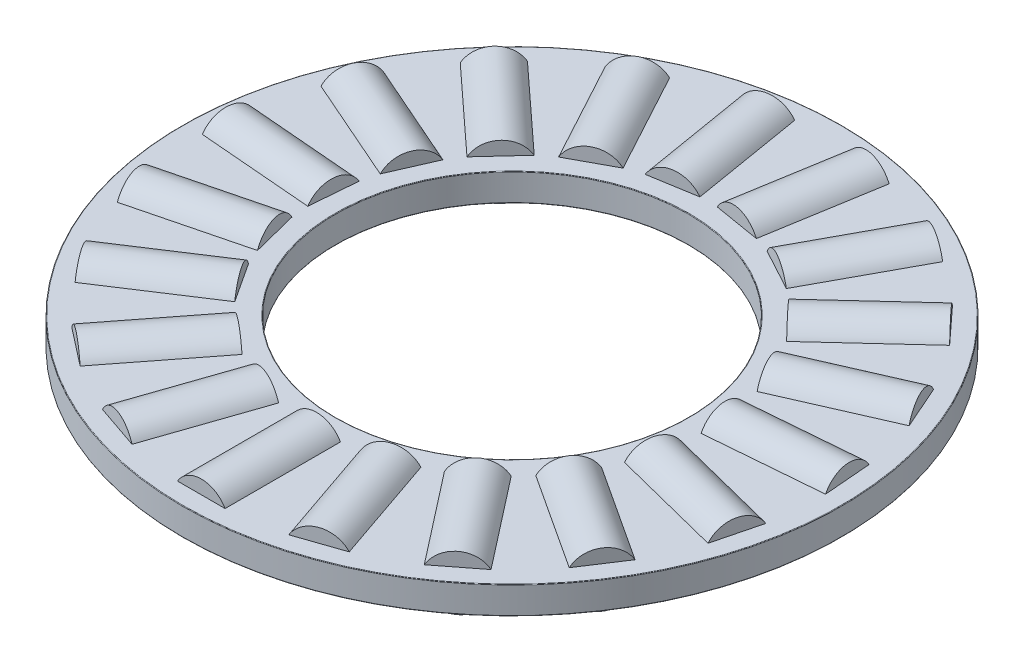
SolidWorks part; units mm, degrees
ref_plane "Front Plane" through (0, 0, 0) normal (0, 0, 1) x (1, 0, 0)
ref_plane "Top Plane" through (0, 0, 0) normal (0, 1, 0) x (1, 0, 0)
ref_plane "Right Plane" through (0, 0, 0) normal (1, 0, 0) x (0, 0, -1)
sketch "Sketch1" plane through (0, 0, 0) normal (1, 0, 0) x (0, 0, -1)
  line L0 (-11.9062, 0) -> (11.9062, 0) construction
  line L1 (0, -0.9922) -> (0, 0.9922) construction
  line L2 (-11.9063, 0.4961) -> (-6.3754, 0.4961)
  line L3 (-11.9063, 0.4961) -> (-11.9063, -0.4961)
  line L4 (-11.9063, -0.4961) -> (-6.3754, -0.4961)
  line L5 (-6.3754, 0.4961) -> (-6.3754, -0.4961)
  line L7 (-9.1408, 0.9922) -> (-9.1408, 0.4961) construction
  line L8 (-11.2244, 0.9922) -> (-7.0572, 0.9922) construction
  line L9 (-11.2244, 0.9922) -> (-11.2244, -0.9922) construction
  line L10 (-11.2244, -0.9922) -> (-7.0572, -0.9922) construction
  line L11 (-7.0572, 0.9922) -> (-7.0572, -0.9922) construction
  point P16 (-11.2244, 0)
  dimension "OD" = 23.8125
  dimension "Shaft Dia" = 12.7508
  dimension "Th" = 1.9844
  dimension "D2" = 0.9922
  dimension "D1" = 4.1672
  dimension "D3" = 5.5309
revolve "Revolve1" add sketch "Sketch1" angle 360 about L1
sketch "Sketch3" plane through (0, 0, 0) normal (1, 0, 0) x (0, 0, -1)
  line L0 (-11.2244, 0.9922) -> (-11.2244, -0.9922) construction
  line L1 (-11.2244, 0) -> (-7.0572, 0)
  line L2 (-11.2244, 0) -> (-11.2244, 0.9922)
  line L3 (-11.2244, 0.9922) -> (-7.0572, 0.9922)
  line L4 (-7.0572, 0) -> (-7.0572, 0.9922)
revolve "Cut-Revolve1" cut sketch "Sketch3" angle 360 about L1
sketch "Sketch2" plane through (0, 0, 0) normal (1, 0, 0) x (0, 0, -1)
  line L1 (-11.2244, 0) -> (-7.0572, 0)
  line L2 (-11.2244, 0) -> (-11.2244, 0.9922)
  line L3 (-11.2244, 0.9922) -> (-7.0572, 0.9922)
  line L4 (-7.0572, 0) -> (-7.0572, 0.9922)
revolve "Revolve2" add sketch "Sketch2" angle 360 about L1
ref_axis "Axis1" through (0, 0.9922, 0) along (0, -1, 0)
pattern_circular "CirPattern1" count 19 every 18.947 about axis through (0, 0.9922, 0) along (0, -1, 0) of bodies 187 411
pattern_circular "CirPattern2" count 19 every 18.947 about axis through (0, 0, 0) along (0, 1, 0) of "Cut-Revolve1"
sketch "Sketch4" plane through (0, 0, 0) normal (1, 0, 0) x (0, 0, -1)
  line L0 (-11.9063, 0.4961) -> (-11.9063, -0.4961) construction
  line L1 (-11.9062, 9.1091) -> (-6.35, 9.1091)
  line L2 (-11.9062, 9.1091) -> (-11.9062, 9.9219)
  line L3 (-11.9062, 9.9219) -> (-6.35, 9.9219)
  line L4 (-6.35, 9.1091) -> (-6.35, 9.9219)
  line L5 (-11.9062, -9.9219) -> (-6.3754, -9.9219)
  line L6 (-11.9062, -9.9219) -> (-11.9062, -9.1091)
  line L7 (-11.9062, -9.1091) -> (-6.3754, -9.1091)
  line L8 (-6.3754, -9.9219) -> (-6.3754, -9.1091)
  line L10 (-6.3754, 0.4961) -> (-6.3754, -0.4961) construction
  line L11 (0, 0) -> (-11.9062, 0) construction
  line L12 (-11.9062, 0) -> (11.9062, 0) construction
  line L13 (0, -0.9922) -> (0, 0.9922) construction
  dimension "Ht" = 19.8438
  dimension "Washer Th" = 0.8128
  dimension "Washer ID" = 12.7
  dimension "Washer OD" = 23.8125
fillet "Fillet2" radius 0.0198 4 edges at (0, -0.4961, -6.3754) (0, 0.4961, -6.3754) (0, -0.4961, -11.9063) (0, 0.4961, -11.9063)
equation "\"D2@Sketch1\"= \"Th@Sketch1\" * .5"
equation "\"Rollers@CirPattern1\"= \"OD@Sketch1\" * 20"
equation "\"Angle@CirPattern1\" = 360/\"Rollers@CirPattern1\""
equation "\"D1@CirPattern2\" = \"Rollers@CirPattern1\""
equation "\"D2@CirPattern2\" = \"Angle@CirPattern1\""
equation "\"Ht@Sketch4\" = \"Th@Sketch1\"*10"
